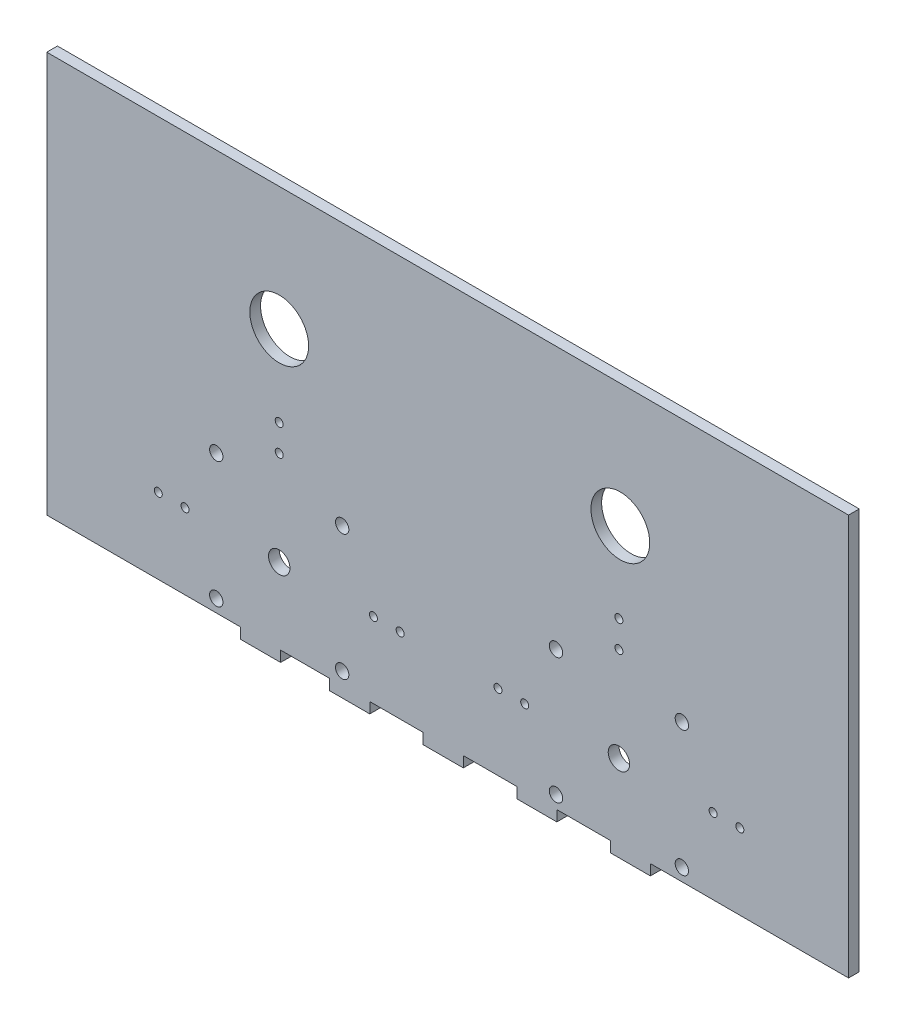
SolidWorks part; units mm, degrees
material "1060 Alloy"
ref_plane "Front Plane" through (0, 0, 0) normal (0, 0, 1) x (1, 0, 0)
ref_plane "Top Plane" through (0, 0, 0) normal (0, 1, 0) x (1, 0, 0)
ref_plane "Right Plane" through (0, 0, 0) normal (1, 0, 0) x (0, 0, -1)
sketch "Sketch1" plane through (0, 0, 0) normal (0, 0, 1) x (1, 0, 0)
  line L0 (-150.5285, 102.6634) -> (149.4715, 102.6634)
  line L2 (-150.5285, -47.3366) -> (-150.5285, 102.6634)
  line L3 (-44.6687, -51.3366) -> (-44.6687, -47.3366)
  line L4 (40, 4.4634) -> (87.1, 4.4634) construction
  line L5 (-44.6687, -47.3366) -> (-63.0285, -47.3366)
  line L6 (-63.0285, -47.3366) -> (-63.0285, -51.3366)
  line L21 (149.4715, -47.3366) -> (149.4715, 102.6634)
  line L24 (-87.1, -42.6366) -> (-40, -42.6366) construction
  line L25 (-87.1, 4.4634) -> (-87.1, -42.6366) construction
  line L27 (75.3313, -47.3366) -> (75.3313, -51.3366)
  line L28 (60.3313, -51.3366) -> (75.3313, -51.3366)
  line L29 (60.3313, -47.3366) -> (60.3313, -51.3366)
  line L30 (40.3313, -47.3366) -> (40.3313, -51.3366)
  line L31 (25.3313, -51.3366) -> (40.3313, -51.3366)
  line L32 (25.3313, -47.3366) -> (25.3313, -51.3366)
  line L33 (75.3313, -47.3366) -> (149.4715, -47.3366)
  line L34 (-29.6687, -47.3366) -> (-29.6687, -51.3366)
  line L35 (-44.6687, -51.3366) -> (-29.6687, -51.3366)
  line L37 (5.3313, -47.3366) -> (25.3313, -47.3366)
  line L38 (5.3313, -47.3366) -> (5.3313, -51.3366)
  line L39 (-9.6687, -51.3366) -> (5.3313, -51.3366)
  line L40 (-9.6687, -47.3366) -> (-9.6687, -51.3366)
  line L41 (40.3313, -47.3366) -> (60.3313, -47.3366)
  line L43 (-78.0285, -51.3366) -> (-63.0285, -51.3366)
  line L44 (-78.0285, -47.3366) -> (-78.0285, -51.3366)
  line L45 (-29.6687, -47.3366) -> (-9.6687, -47.3366)
  line L47 (-150.5285, -47.3366) -> (-78.0285, -47.3366)
  line L48 (-40, 4.4634) -> (-87.1, -42.6366) construction
  line L49 (-40, -42.6366) -> (-40, 4.4634) construction
  line L50 (-40, 4.4634) -> (-87.1, 4.4634) construction
  line L57 (87.1, 4.4634) -> (87.1, -42.6366) construction
  line L58 (87.1, -42.6366) -> (40, -42.6366) construction
  line L59 (40, -42.6366) -> (40, 4.4634) construction
  line L60 (40, 4.4634) -> (87.1, -42.6366) construction
  line L61 (87.1, 4.4634) -> (40, -42.6366) construction
  circle A0 centre (-63.55, 16.1634) radius 1.5
  circle A1 centre (-63.55, 26.1634) radius 1.5
  circle A2 centre (-98.8, -19.0866) radius 1.5
  circle A3 centre (-108.8, -19.0866) radius 1.5
  circle A4 centre (63.55, 16.1634) radius 1.5
  circle A5 centre (63.55, 26.1634) radius 1.5
  circle A6 centre (98.8, -19.0334) radius 1.5
  circle A7 centre (108.8, -19.0334) radius 1.5
  circle A8 centre (64.0785, 56.4643) radius 11
  circle A9 centre (-63.55, 56.4643) radius 11
  circle A10 centre (-28.3, -19.0866) radius 1.5
  circle A11 centre (-18.3, -19.0866) radius 1.5
  circle A12 centre (28.3, -19.0866) radius 1.5
  circle A13 centre (18.3, -19.0866) radius 1.5
  circle A14 centre (63.55, -19.0866) radius 4
  circle A15 centre (40, 4.4634) radius 2.5
  circle A16 centre (40, -42.6366) radius 2.5
  circle A17 centre (87.1, 4.4634) radius 2.5
  circle A18 centre (87.1, -42.6366) radius 2.5
  circle A19 centre (-40, -42.6366) radius 2.5
  circle A20 centre (-87.1, 4.4634) radius 2.5
  circle A21 centre (-87.1, -42.6366) radius 2.5
  circle A22 centre (-63.55, -19.0866) radius 4
  circle A23 centre (-40, 4.4634) radius 2.5
  point P9 (-63.55, 4.4634)
  point P12 (63.55, 4.4634)
  point P51 (63.55, -19.0866)
  dimension "D15" = 10
  dimension "D17" = 11.7
  dimension "D19" = 11.7
  dimension "D23" = 8
  dimension "D27" = 5
  dimension "D12" = 11.7
  dimension "D5" = 10
  dimension "D3" = 4
  dimension "D4" = 40
  dimension "D6" = 11.7
  dimension "D7" = 11.7
  dimension "D8" = 150
  dimension "D9" = 11.7
  dimension "D10" = 15
  dimension "D11" = 80
  dimension "D13" = 10
  dimension "D14" = 4.7
  dimension "D16" = 10
  dimension "D18" = 10
  dimension "D20" = 10
  dimension "D21" = 47.1
extrude "Boss-Extrude2" add sketch "Sketch1" along normal blind 4
